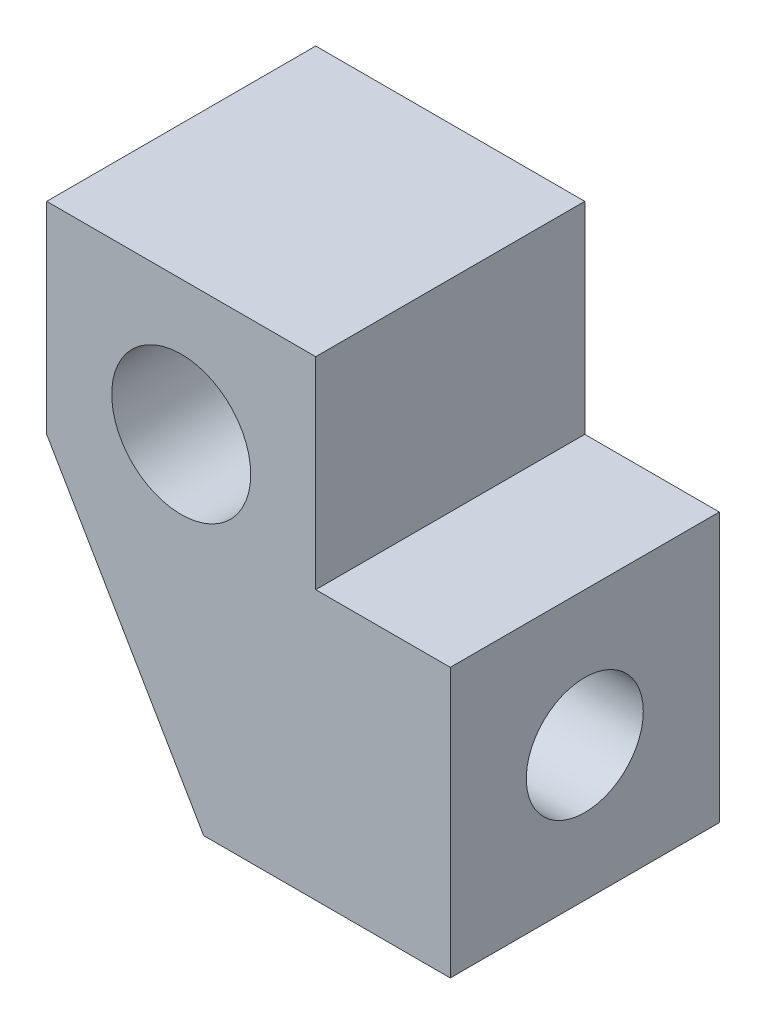
SolidWorks part; units mm, degrees
ref_plane "Front Plane" through (0, 0, 0) normal (0, 0, 1) x (1, 0, 0)
ref_plane "Top Plane" through (0, 0, 0) normal (0, 1, 0) x (1, 0, 0)
ref_plane "Right Plane" through (0, 0, 0) normal (1, 0, 0) x (0, 0, -1)
sketch "Sketch1" plane through (0, 0, 0) normal (0, 0, 1) x (1, 0, 0)
  line L0 (48, -38) -> (45, -38)
  line L1 (-48, -44) -> (39, -44) construction
  line L2 (-48, -44) -> (-48, 44) construction
  line L3 (-48, 44) -> (48, 44) construction
  line L4 (48, -44) -> (48, 44) construction
  line L5 (-48, -44) -> (48, 44) construction
  line L6 (-48, 44) -> (48, -44) construction
  line L7 (-42, -36.5) -> (42, -36.5) construction
  line L8 (-42, -36.5) -> (-42, 36.5) construction
  line L9 (-42, 36.5) -> (42, 36.5) construction
  line L10 (42, -36.5) -> (42, 36.5) construction
  line L11 (-42, -36.5) -> (42, 36.5) construction
  line L12 (-42, 36.5) -> (42, -36.5) construction
  line L17 (45, -38) -> (45, -33.5)
  line L18 (45, -33.5) -> (39, -33.5)
  line L19 (39, -33.5) -> (39, -38)
  line L20 (42.5, -44) -> (48, -44)
  line L21 (48, -44) -> (48, -38)
  line L22 (39, -38) -> (42.5, -44)
  line L23 (42.5, -44) -> (48, -44) construction
  circle A0 centre (42, -36.5) radius 1.55
  point P0 (0, 0)
  point P6 (0, 0)
  point P16 (42.5, -34.5)
  dimension "D5" = 3.1
  dimension "D1" = 73
  dimension "D2" = 84
  dimension "D3" = 96
  dimension "D4" = 88
  dimension "D6" = 3
  dimension "D7" = 6
  dimension "D8" = 3
  dimension "D9" = 3
  dimension "D10" = 6
extrude "Boss-Extrude1" add sketch "Sketch1" along normal blind 6
sketch "Sketch3" plane through (48, 0, 0) normal (1, 0, 0) x (0, 0, -1)
  line L0 (-6, -44) -> (0, -38) construction
  line L1 (0, -38) -> (0, -44) construction
  line L2 (0, -44) -> (-6, -38) construction
  circle A0 centre (-3, -41) radius 1.305
  point P11 (-3, -41)
  dimension "D1" = 2.61
extrude "Cut-Extrude3" cut sketch "Sketch3" against normal through all
equation "\"D8@Sketch1\"=\"D6@Sketch1\""
equation "\"D9@Sketch1\"=\"D6@Sketch1\""
equation "\"D10@Sketch1\"=\"D7@Sketch1\""
